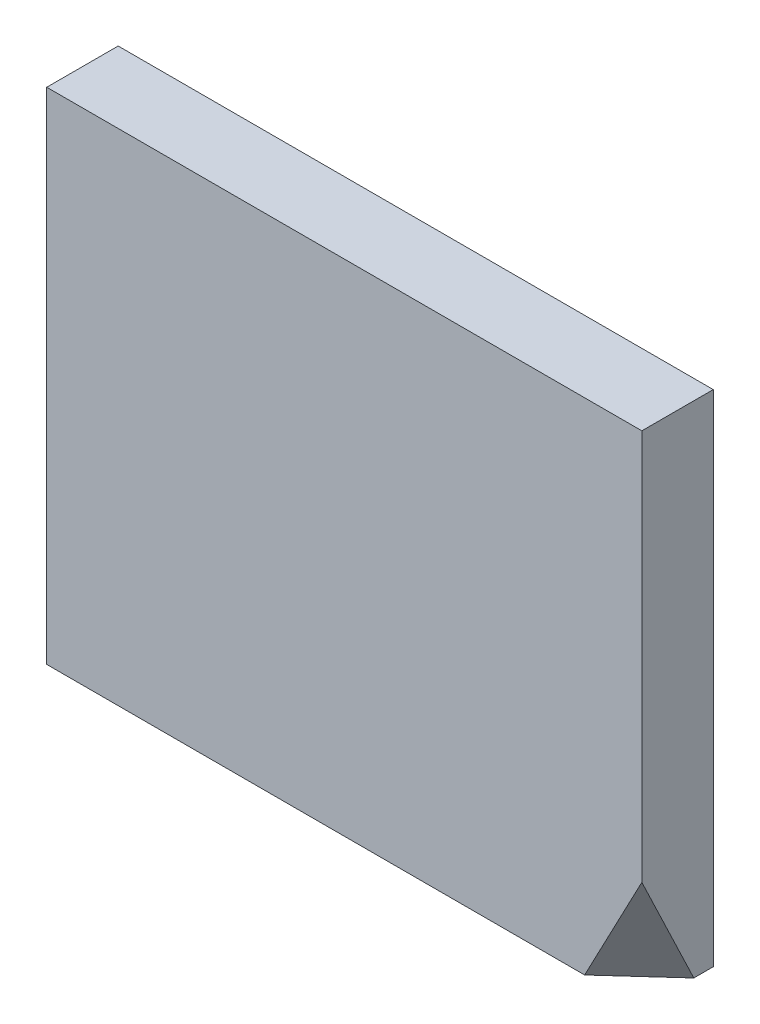
SolidWorks part; units mm, degrees
material "Стекло"
ref_plane "Front" through (0, 0, 0) normal (0, 0, 1) x (1, 0, 0)
ref_plane "Top" through (0, 0, 0) normal (0, 1, 0) x (1, 0, 0)
ref_plane "Right" through (0, 0, 0) normal (1, 0, 0) x (0, 0, -1)
sketch "Эскиз1" plane through (0, 0, 0) normal (0, 0, 1) x (1, 0, 0)
  line L0 (-12.5, -10.5) -> (12.5, -10.5)
  line L1 (12.5, -10.5) -> (12.5, 10.5)
  line L2 (12.5, 10.5) -> (-12.5, 10.5)
  line L3 (-12.5, 10.5) -> (-12.5, -10.5)
  dimension "D1" = 21
  dimension "D2" = 25
  dimension "D3" = 12.5
  dimension "D4" = 10.5
extrude "Вытянуть1" add sketch "Эскиз1" along normal blind 3
chamfer "Фаска2" [suppressed] distance 3 angle 45
chamfer "Фаска3" [suppressed] distance 4 angle 30
chamfer "Фаска4" [suppressed] distance 4 angle 30
chamfer "Фаска5" [suppressed] distance 1 angle 45
chamfer "Фаска1" [suppressed] distance 0.3 angle 45
ref_point "Точка1" parameters "D1"=11
ref_point "Точка2" parameters "D1"=9.5
ref_plane "Плоскость1" through (2.321, -2.0045, -3.0667) normal (-0.5352, 0.4622, 0.7071) x (0.8322, 0.1449, 0.5352)
sketch "Эскиз5" plane through (2.321, -2.0045, -3.0667) normal (-0.5352, 0.4622, 0.7071) x (0.8322, 0.1449, 0.5352)
  line L0 (11.1495, -4.7616) -> (8.4871, -9.1098)
  line L1 (10.4871, -8.7616) -> (13.5297, 9.6107) construction
  line L2 (-10.3188, -12.3838) -> (10.4871, -8.7616) construction
  dimension "D1" = 2
  dimension "D2" = 4
extrude "Вырез-Вытянуть3" cut sketch "Эскиз5" against normal through all and the other way through all
